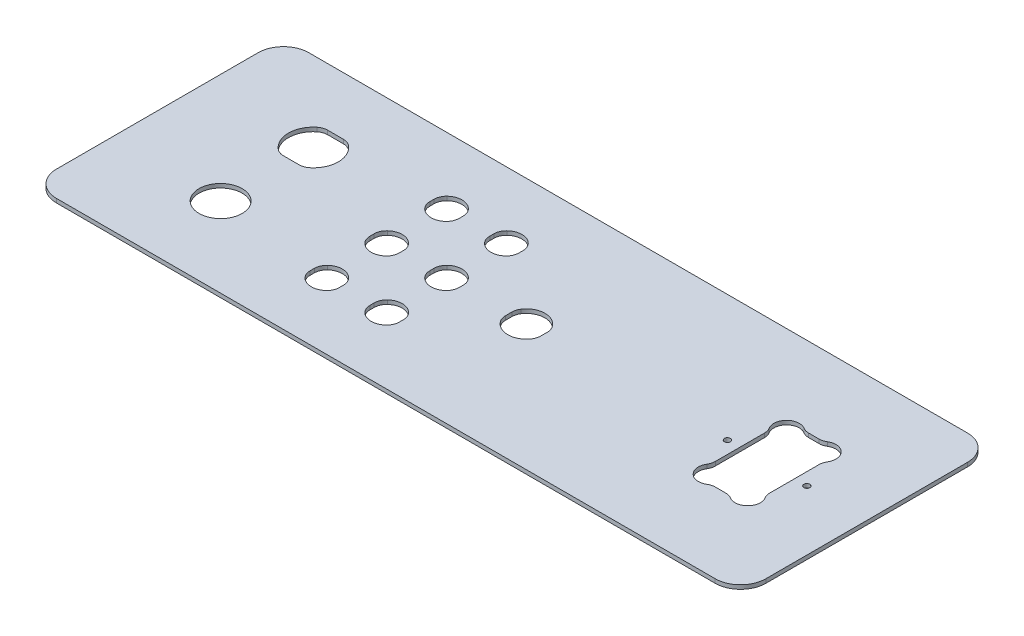
SolidWorks part; units mm, degrees
ref_plane "Front Plane" through (0, 0, 0) normal (0, 0, 1) x (1, 0, 0)
ref_plane "Top Plane" through (0, 0, 0) normal (0, 1, 0) x (1, 0, 0)
ref_plane "Right Plane" through (0, 0, 0) normal (1, 0, 0) x (0, 0, -1)
sketch "Sketch1" plane through (0, 0, 0) normal (0, 1, 0) x (1, 0, 0)
  line L0 (-118.8936, 34.346) -> (-126.7064, 34.346)
  line L1 (-165.1, 63.246) -> (165.1, 63.246)
  line L2 (-177.8, 50.546) -> (-177.8, -50.546)
  line L3 (-165.1, -63.246) -> (165.1, -63.246)
  line L4 (177.8, 50.546) -> (177.8, -50.546)
  line L5 (-126.7064, 12.146) -> (-118.8936, 12.146)
  line L6 (-62.8, 63.246) -> (-62.8, 30) construction
  line L7 (-62.8, 30) -> (-62.8, 0) construction
  line L8 (-62.8, 0) -> (-62.8, -30) construction
  line L9 (-62.8, -30) -> (-62.8, -63.246) construction
  line L10 (-62.8, -30) -> (-32.8, -30) construction
  line L11 (-62.8, 0) -> (-32.8, 0) construction
  line L12 (-62.8, 30) -> (-32.8, 30) construction
  line L13 (-70.115, 31.0143) -> (-70.115, 28.9857)
  line L14 (-55.485, 31.0143) -> (-55.485, 28.9857)
  line L15 (-40.115, 31.0143) -> (-40.115, 28.9857)
  line L16 (-25.485, 31.0143) -> (-25.485, 28.9857)
  line L17 (-70.115, 1.0143) -> (-70.115, -1.0143)
  line L18 (-55.485, 1.0143) -> (-55.485, -1.0143)
  line L19 (-70.115, -28.9857) -> (-70.115, -31.0143)
  line L20 (-55.485, -28.9857) -> (-55.485, -31.0143)
  line L21 (-40.115, -28.9857) -> (-40.115, -31.0143)
  line L22 (-25.485, -28.9857) -> (-25.485, -31.0143)
  line L23 (-25.485, 1.0143) -> (-25.485, -1.0143)
  line L24 (-40.115, 1.0143) -> (-40.115, -1.0143)
  line L25 (-1.63, 1.6159) -> (-1.63, -1.6159)
  line L26 (16.03, 1.6159) -> (16.03, -1.6159)
  line L27 (114.215, -14.4347) -> (114.215, -23.415) construction
  line L28 (125.3219, 23.415) -> (130.4681, 23.415)
  line L29 (114.215, 12.3081) -> (114.215, -12.3081)
  line L30 (125.3219, -23.415) -> (130.4681, -23.415)
  line L31 (141.575, 12.3081) -> (141.575, -12.3081)
  line L32 (114.215, -23.415) -> (123.1953, -23.415) construction
  line L33 (132.5947, -23.415) -> (141.575, -23.415) construction
  line L34 (141.575, -23.415) -> (141.575, -14.4347) construction
  line L35 (132.5947, 23.415) -> (141.575, 23.415) construction
  line L36 (141.575, 23.415) -> (141.575, 14.4347) construction
  line L37 (114.215, 14.4347) -> (114.215, 23.415) construction
  line L38 (114.215, 23.415) -> (123.1953, 23.415) construction
  line L39 (114.215, 0) -> (107.99, 0) construction
  line L40 (141.575, 0) -> (147.8, 0) construction
  arc A0 (-177.8, -50.546) -> (-165.1, -63.246) centre (-165.1, -50.546) ccw
  arc A1 (165.1, -63.246) -> (177.8, -50.546) centre (165.1, -50.546) ccw
  arc A2 (165.1, 63.246) -> (177.8, 50.546) centre (165.1, 50.546) cw
  arc A3 (-165.1, 63.246) -> (-177.8, 50.546) centre (-165.1, 50.546) ccw
  circle A4 centre (-122.8, -23.246) radius 10.8
  arc A5 (-130.7398, 32.9005) -> (-130.7398, 13.5915) centre (-122.8, 23.246) ccw
  arc A6 (-114.8602, 13.5915) -> (-114.8602, 32.9005) centre (-122.8, 23.246) ccw
  arc A7 (-126.7064, 12.146) -> (-130.7398, 13.5915) centre (-126.7064, 18.496) cw
  arc A8 (-118.8936, 12.146) -> (-114.8602, 13.5915) centre (-118.8936, 18.496) ccw
  arc A9 (-118.8936, 34.346) -> (-114.8602, 32.9005) centre (-118.8936, 27.996) cw
  arc A10 (-126.7064, 34.346) -> (-130.7398, 32.9005) centre (-126.7064, 27.996) ccw
  arc A11 (-57.458, 35.6148) -> (-68.142, 35.6148) centre (-62.8, 30) ccw
  arc A12 (-38.142, 24.3852) -> (-27.458, 24.3852) centre (-32.8, 30) ccw
  arc A13 (-38.142, -5.6148) -> (-27.458, -5.6148) centre (-32.8, 0) ccw
  arc A14 (-68.142, -5.6148) -> (-57.458, -5.6148) centre (-62.8, 0) ccw
  arc A15 (-57.458, -24.3852) -> (-68.142, -24.3852) centre (-62.8, -30) ccw
  arc A16 (-27.458, -24.3852) -> (-38.142, -24.3852) centre (-32.8, -30) ccw
  arc A17 (-57.458, 5.6148) -> (-68.142, 5.6148) centre (-62.8, 0) ccw
  arc A18 (-68.142, -35.6148) -> (-57.458, -35.6148) centre (-62.8, -30) ccw
  arc A19 (-38.142, -35.6148) -> (-27.458, -35.6148) centre (-32.8, -30) ccw
  arc A20 (-27.458, 5.6148) -> (-38.142, 5.6148) centre (-32.8, 0) ccw
  arc A21 (-27.458, 35.6148) -> (-38.142, 35.6148) centre (-32.8, 30) ccw
  arc A22 (-68.142, 24.3852) -> (-57.458, 24.3852) centre (-62.8, 30) ccw
  arc A23 (-38.142, -35.6148) -> (-40.115, -31.0143) centre (-33.765, -31.0143) cw
  arc A24 (-27.458, -35.6148) -> (-25.485, -31.0143) centre (-31.835, -31.0143) ccw
  arc A25 (-25.485, -28.9857) -> (-27.458, -24.3852) centre (-31.835, -28.9857) ccw
  arc A26 (-40.115, -28.9857) -> (-38.142, -24.3852) centre (-33.765, -28.9857) cw
  arc A27 (-70.115, -31.0143) -> (-68.142, -35.6148) centre (-63.765, -31.0143) ccw
  arc A28 (-55.485, -31.0143) -> (-57.458, -35.6148) centre (-61.835, -31.0143) cw
  arc A29 (-57.458, -24.3852) -> (-55.485, -28.9857) centre (-61.835, -28.9857) cw
  arc A30 (-68.142, -24.3852) -> (-70.115, -28.9857) centre (-63.765, -28.9857) ccw
  arc A31 (-68.142, -5.6148) -> (-70.115, -1.0143) centre (-63.765, -1.0143) cw
  arc A32 (-70.115, 1.0143) -> (-68.142, 5.6148) centre (-63.765, 1.0143) cw
  arc A33 (-55.485, 1.0143) -> (-57.458, 5.6148) centre (-61.835, 1.0143) ccw
  arc A34 (-57.458, -5.6148) -> (-55.485, -1.0143) centre (-61.835, -1.0143) ccw
  arc A35 (-40.115, -1.0143) -> (-38.142, -5.6148) centre (-33.765, -1.0143) ccw
  arc A36 (-25.485, -1.0143) -> (-27.458, -5.6148) centre (-31.835, -1.0143) cw
  arc A37 (-27.458, 5.6148) -> (-25.485, 1.0143) centre (-31.835, 1.0143) cw
  arc A38 (-40.115, 1.0143) -> (-38.142, 5.6148) centre (-33.765, 1.0143) cw
  arc A39 (-40.115, 28.9857) -> (-38.142, 24.3852) centre (-33.765, 28.9857) ccw
  arc A40 (-25.485, 28.9857) -> (-27.458, 24.3852) centre (-31.835, 28.9857) cw
  arc A41 (-25.485, 31.0143) -> (-27.458, 35.6148) centre (-31.835, 31.0143) ccw
  arc A42 (-40.115, 31.0143) -> (-38.142, 35.6148) centre (-33.765, 31.0143) cw
  arc A43 (-55.485, 31.0143) -> (-57.458, 35.6148) centre (-61.835, 31.0143) ccw
  arc A44 (-55.485, 28.9857) -> (-57.458, 24.3852) centre (-61.835, 28.9857) cw
  arc A45 (-70.115, 28.9857) -> (-68.142, 24.3852) centre (-63.765, 28.9857) ccw
  arc A46 (-70.115, 31.0143) -> (-68.142, 35.6148) centre (-63.765, 31.0143) cw
  arc A47 (-0.6003, -5.0825) -> (15.0003, -5.0825) centre (7.2, 0) ccw
  arc A48 (15.0003, 5.0825) -> (-0.6003, 5.0825) centre (7.2, 0) ccw
  arc A49 (-1.63, -1.6159) -> (-0.6003, -5.0825) centre (4.72, -1.6159) ccw
  arc A50 (16.03, -1.6159) -> (15.0003, -5.0825) centre (9.68, -1.6159) cw
  arc A51 (16.03, 1.6159) -> (15.0003, 5.0825) centre (9.68, 1.6159) ccw
  arc A52 (-1.63, 1.6159) -> (-0.6003, 5.0825) centre (4.72, 1.6159) cw
  arc A53 (122.0135, 24.3449) -> (113.2851, 15.6165) centre (118.7051, 18.9249) ccw
  arc A54 (142.5049, 15.6165) -> (133.7765, 24.3449) centre (137.0849, 18.9249) ccw
  arc A55 (133.7765, -24.3449) -> (142.5049, -15.6165) centre (137.0849, -18.9249) ccw
  arc A56 (113.2851, -15.6165) -> (122.0135, -24.3449) centre (118.7051, -18.9249) ccw
  circle A57 centre (107.99, 0) radius 1.5
  circle A58 centre (147.8, 0) radius 1.5
  arc A59 (142.5049, -15.6165) -> (141.575, -12.3081) centre (147.925, -12.3081) cw
  arc A60 (133.7765, -24.3449) -> (130.4681, -23.415) centre (130.4681, -29.765) ccw
  arc A61 (125.3219, -23.415) -> (122.0135, -24.3449) centre (125.3219, -29.765) ccw
  arc A62 (114.215, -12.3081) -> (113.2851, -15.6165) centre (107.865, -12.3081) cw
  arc A63 (113.2851, 15.6165) -> (114.215, 12.3081) centre (107.865, 12.3081) cw
  arc A64 (142.5049, 15.6165) -> (141.575, 12.3081) centre (147.925, 12.3081) ccw
  arc A65 (133.7765, 24.3449) -> (130.4681, 23.415) centre (130.4681, 29.765) cw
  arc A66 (122.0135, 24.3449) -> (125.3219, 23.415) centre (125.3219, 29.765) ccw
  point P4 (-177.8, 0)
  point P5 (0, 63.246)
  point P11 (-177.8, -63.246)
  point P16 (177.8, 63.246)
  point P19 (-177.8, 63.246)
  point P29 (-117.052, 12.146)
  point P38 (141.575, -14.4347)
  point P75 (-40.115, -32.5599)
  point P84 (-70.115, -32.5599)
  point P89 (-55.485, -27.4401)
  point P92 (-70.115, -27.4401)
  point P99 (-55.485, 2.5599)
  point P108 (-25.485, 2.5599)
  point P111 (-40.115, 2.5599)
  point P118 (-25.485, 32.5599)
  point P127 (-70.115, 27.4401)
  point P135 (16.03, 2.9508)
  point P184 (110.4465, -17.2446)
  point P185 (0, 0)
  point P186 (140.3756, -16.0549)
  point P187 (142.4805, -16.0545)
  point P188 (0, 0)
  point P189 (0, 0)
  dimension "D3" = 12.7
  dimension "D4" = 55
  dimension "D6" = 21.6
  dimension "D7" = 40
  dimension "D8" = 25
  dimension "D9" = 6.35
  dimension "D13" = 15.5
  dimension "D15" = 18.62
  dimension "D16" = 17.66
  dimension "D18" = 27.36
  dimension "D20" = 3
  dimension "D22" = 6.35
  dimension "D1" = 126.492
  dimension "D2" = 355.6
  dimension "D5" = 40
  dimension "D10" = 22.2
  dimension "D11" = 30
  dimension "D12" = 60
  dimension "D14" = 14.63
  dimension "D17" = 40
  dimension "D19" = 46.83
  dimension "D21" = 39.81
  dimension "D23" = 30
extrude "Boss-Extrude1" add sketch "Sketch1" along normal blind 2
